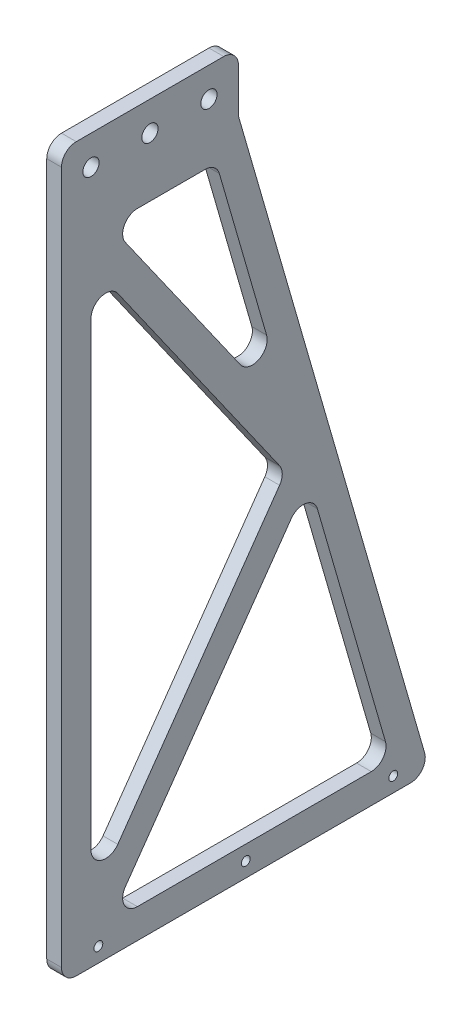
SolidWorks part; units mm, degrees
ref_plane "Front Plane" through (0, 0, 0) normal (0, 0, 1) x (1, 0, 0)
ref_plane "Top Plane" through (0, 0, 0) normal (0, 1, 0) x (1, 0, 0)
ref_plane "Right Plane" through (0, 0, 0) normal (1, 0, 0) x (0, 0, -1)
sketch "Sketch1" plane through (0, 0, 0) normal (1, 0, 0) x (0, 0, -1)
  line L0 (-30, -10) -> (-30, -235)
  line L1 (-30, 10) -> (30, 10)
  line L2 (-30, 10) -> (-30, -10)
  line L3 (-30, -10) -> (30, -10)
  line L4 (30, 10) -> (30, -10)
  line L5 (-30, 10) -> (30, -10) construction
  line L6 (-30, -10) -> (30, 10) construction
  line L7 (-30, -235) -> (95, -235)
  line L8 (30, -10) -> (95, -235)
  line L9 (-20, -20) -> (22.48, -20)
  line L10 (22.48, -20) -> (81.7022, -225)
  line L11 (-20, -225) -> (81.7022, -225)
  line L12 (-20, -20) -> (-20, -225)
  line L13 (-20, -225) -> (52.0911, -122.5) construction
  line L14 (52.0911, -122.5) -> (-20, -20) construction
  line L15 (-15.9102, -227.8764) -> (58.2039, -122.5)
  line L16 (58.2039, -122.5) -> (-15.9102, -17.1236)
  line L17 (-24.0898, -222.1236) -> (45.9782, -122.5)
  line L18 (45.9782, -122.5) -> (-24.0898, -22.8764)
  line L19 (-17.5, -230) -> (82.5, -230) construction
  line L20 (32.5, -235) -> (32.5, -225) construction
  circle A0 centre (82.5, -230) radius 1.5
  circle A1 centre (-17.5, -230) radius 1.5
  circle A2 centre (32.5, -230) radius 1.5
  point P0 (0, 0)
  point P23 (32.5, -230)
  point P24 (32.5, -235)
  point P29 (0, 0)
  point P30 (32.5, -230.3644)
  point P31 (32.5, -230)
  dimension "D8" = 3
  dimension "D1" = 60
  dimension "D2" = 20
  dimension "D3" = 225
  dimension "D4" = 125
  dimension "D9" = 100
  dimension "D5" = 10
  dimension "D6" = 5
  dimension "D7" = 5
extrude "Boss-Extrude1" add sketch "Sketch1" along normal blind 5
hole_wizard "M5 Clearance Hole1" positions "Sketch2" profile "Sketch3" hole size "M5" standard "ANSI Metric" end condition through all
sketch "Sketch2" plane through (5, 0, 0) normal (1, 0, 0) x (0, 0, -1)
  line L0 (-20, 0) -> (20, 0)
  point P0 (0, 0)
  point P3 (20, 0)
  point P5 (-20, 0)
  point P12 (0, 0)
  dimension "D1" = 40
sketch "Sketch3" plane through (5, 0, 0) normal (0, 1, 0) x (0, 0, -1)
  line L0 (0, 0) -> (0, 5)
  line L1 (0, 5) -> (2.75, 5)
  line L2 (2.75, 5) -> (2.75, 0)
  line L5 (2.75, 0) -> (0, 0)
  line L11 (0, -6.35) -> (0, 107.95) construction
  dimension "Thru Hole Dia." = 5.5
  dimension "Thru Hole Depth" = 5
fillet "Fillet2" radius 5 14 edges at (2.5, -235, 30) (2.5, 10, 30) (2.5, 10, -30) (2.5, -10, -30) (2.5, -216.3087, 20) (2.5, -122.5, -45.9782) (2.5, -28.6913, 20) (2.5, -20, -22.48) (2.5, -20, 13.8872) (2.5, -107.7503, -47.8301) (2.5, -225, 13.8872) (2.5, -225, -81.7022) (2.5, -128.6608, -53.8709) (2.5, -235, -95)
